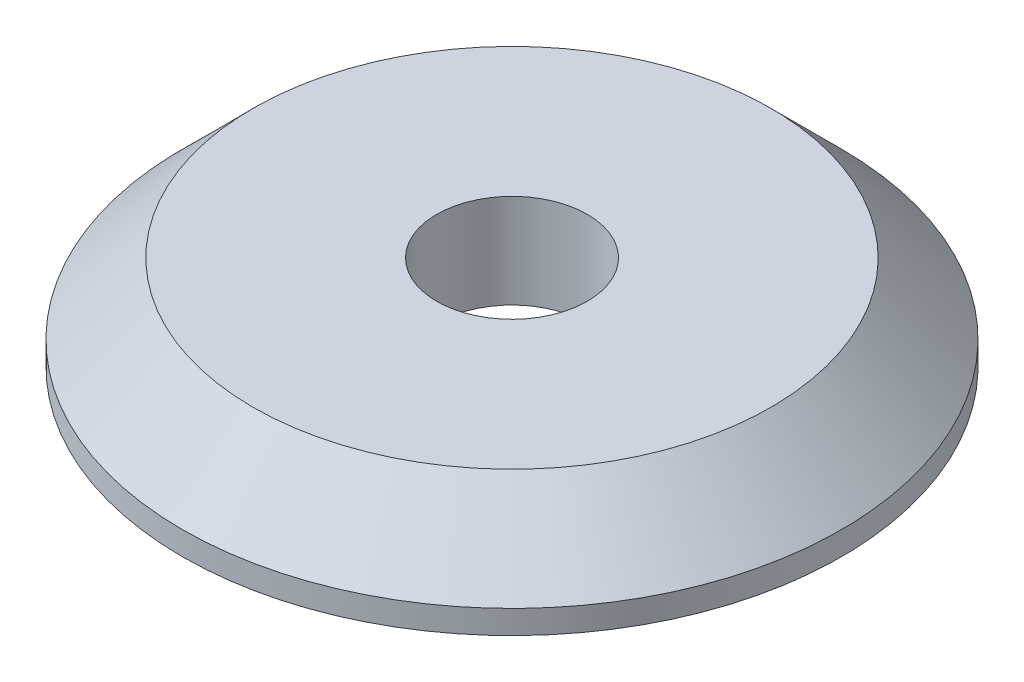
SolidWorks part; units mm, degrees
material "ABS"
ref_plane "Спереди" through (0, 0, 0) normal (0, 0, 1) x (1, 0, 0)
ref_plane "Сверху" through (0, 0, 0) normal (0, 1, 0) x (1, 0, 0)
ref_plane "Справа" through (0, 0, 0) normal (1, 0, 0) x (0, 0, -1)
sketch "Эскиз1" plane through (0, 0, 0) normal (0, 1, 0) x (1, 0, 0)
  circle A0 centre (0, 0) radius 7
  dimension "D1" = 14
extrude "Бобышка-Вытянуть1" add sketch "Эскиз1" along normal blind 2
chamfer "Фаска1" distance 1.5 angle 45 1 edges at (0, 2, 7)
sketch "Эскиз2" plane through (0, 0, 0) normal (0, -1, 0) x (1, 0, 0)
  circle A0 centre (0, 0) radius 1.6
  dimension "D1" = 3.2
extrude "Вырез-Вытянуть1" cut sketch "Эскиз2" against normal through all
